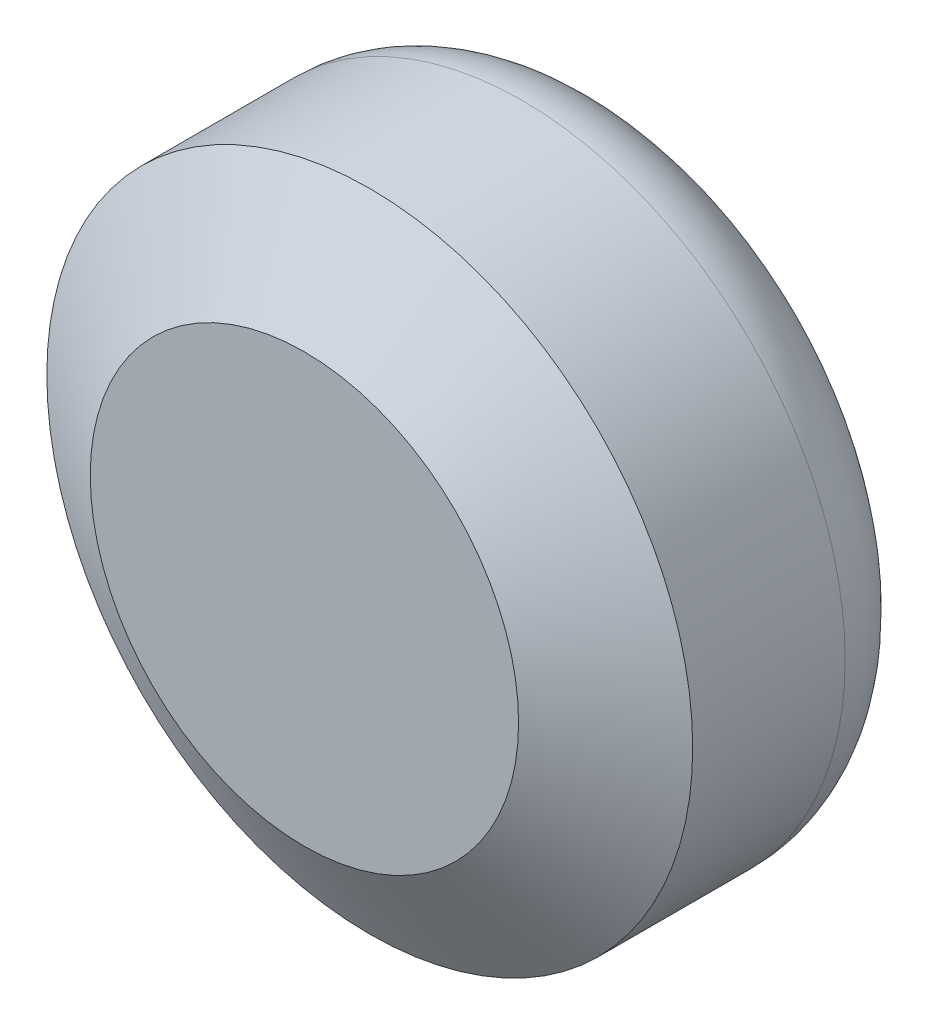
SolidWorks part; units mm, degrees
ref_plane "前视基准面" through (0, 0, 0) normal (0, 0, 1) x (1, 0, 0)
ref_plane "上视基准面" through (0, 0, 0) normal (0, 1, 0) x (1, 0, 0)
ref_plane "右视基准面" through (0, 0, 0) normal (1, 0, 0) x (0, 0, -1)
sketch "草图1" plane through (0, 0, 0) normal (0, 0, 1) x (1, 0, 0)
  circle A0 centre (-35.5777, 22.6225) radius 29.65
  dimension "D1" = 59.3
extrude "凸台-拉伸1" add sketch "草图1" along normal blind 28
chamfer "倒角1" distance 6 angle 59 1 edges at (-5.9277, 22.6225, 28)
fillet "圆角1" radius 8 1 edges at (-5.9277, 22.6225, 0)
